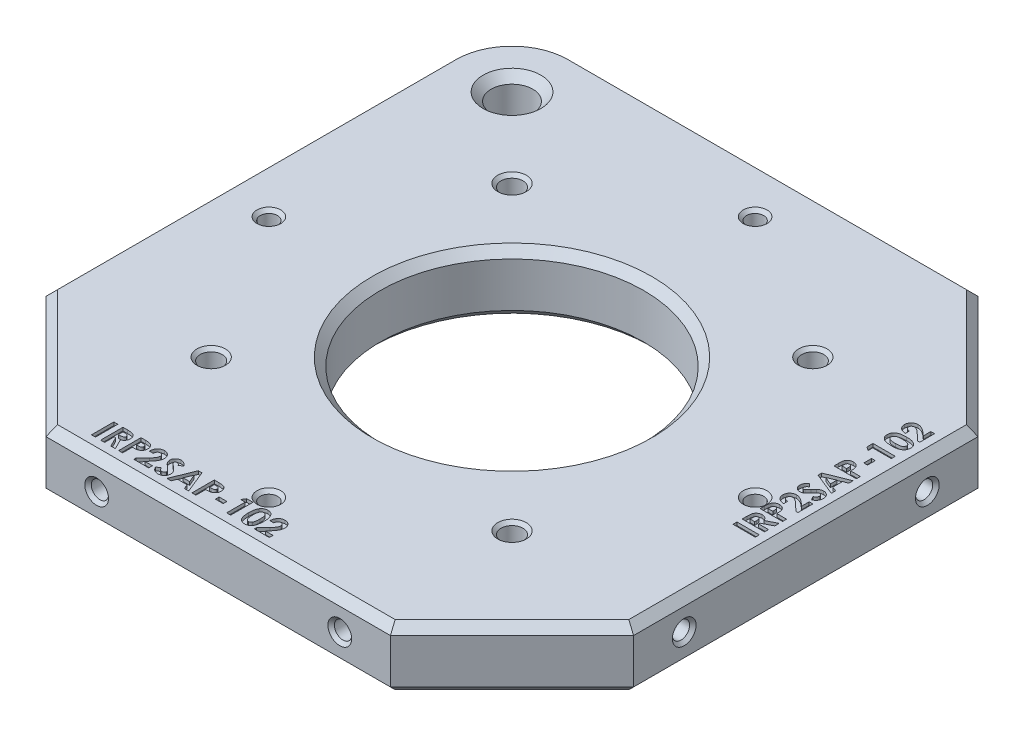
SolidWorks part; units mm, degrees
material "6061-T6 (SS)"
ref_plane "Front" through (0, 0, 0) normal (0, 0, 1) x (1, 0, 0)
ref_plane "Top" through (0, 0, 0) normal (0, 1, 0) x (1, 0, 0)
ref_plane "Right" through (0, 0, 0) normal (1, 0, 0) x (0, 0, -1)
sketch "Sketch1" plane through (0, 0, 0) normal (0, 1, 0) x (1, 0, 0)
  line L0 (0, 46.0375) -> (46.0375, 46.0375) construction
  line L1 (0, 0) -> (92.075, 0)
  line L2 (0, 0) -> (0, 92.075)
  line L3 (0, 92.075) -> (92.075, 92.075)
  line L4 (92.075, 0) -> (92.075, 92.075)
  line L5 (46.0375, 46.0375) -> (46.0375, 92.075) construction
  line L6 (10.033, 82.042) -> (0, 82.042) construction
  line L7 (10.033, 82.042) -> (10.033, 92.075) construction
  line L9 (17.3653, 82.042) -> (13.6992, 88.392) construction
  line L10 (13.6992, 88.392) -> (6.3668, 88.392) construction
  line L11 (6.3668, 88.392) -> (2.7007, 82.042) construction
  line L12 (2.7007, 82.042) -> (6.3668, 75.692) construction
  line L13 (6.3668, 75.692) -> (13.6992, 75.692) construction
  line L14 (13.6992, 75.692) -> (17.3653, 82.042) construction
  circle A0 centre (46.0375, 46.0375) radius 20.6375
  circle A1 centre (10.033, 82.042) radius 4.6037 construction
  circle A2 centre (10.033, 82.042) radius 6.35 construction
  dimension "D2" = 41.275
  dimension "D3" = 9.2075
  dimension "D1" = 92.075
  dimension "D4" = 10.033
  dimension "D5" = 12.7
extrude "Boss-Extrude1" add sketch "Sketch1" along normal blind 9.525
hole_wizard "5/16-18 Tapped Hole1" positions "Sketch9" profile "Sketch10" tap size "5/16-18" standard "ANSI Inch" end condition through all
sketch "Sketch9" plane through (0, 9.525, 0) normal (0, 1, 0) x (1, 0, 0)
  circle A0 centre (10.033, 82.042) radius 4.6037 construction
  point P0 (10.033, 82.042)
sketch "Sketch10" plane through (10.033, 9.525, -82.042) normal (1, 0, 0) x (0, 0, 1)
  line L0 (0, 0) -> (0, 9.525)
  line L1 (0, 9.525) -> (3.2639, 9.525)
  line L2 (3.2639, 9.525) -> (3.2639, 0)
  line L5 (3.2639, 0) -> (0, 0)
  line L11 (0, -6.35) -> (0, 107.95) construction
  dimension "Thru Tap Drill Dia." = 6.5278
  dimension "Thru Tap Drill Depth" = 9.525
cosmetic thread "Hole Thread13" parameters "D2"=7.9375
chamfer "Chamfer1" distance 19.05 angle 45 3 edges at (92.075, 4.7625, 0) (0, 4.7625, 0) (92.075, 4.7625, -92.075)
hole_wizard "#6-32 Tapped Hole1" positions "Sketch2" profile "Sketch3" tap size "#6-32" standard "ANSI Inch"
sketch "Sketch2" plane through (0, 0, 0) normal (0, 0, 1) x (1, 0, 0)
  line L6 (0, 4.7625) -> (26.9875, 4.7625) construction
  line L7 (0, 9.525) -> (0, 0) construction
  line L8 (26.9875, 4.7625) -> (65.0875, 4.7625) construction
  line L9 (65.0875, 4.7625) -> (92.075, 4.7625) construction
  line L10 (92.075, 9.525) -> (92.075, 0) construction
  point P26 (26.9875, 4.7625)
  point P30 (65.0875, 4.7625)
  dimension "D1" = 38.1
sketch "Sketch3" plane through (65.0875, 4.7625, 0) normal (1, 0, 0) x (0, -1, 0)
  line L0 (0, 0) -> (0, 13.5127)
  line L1 (0, 13.5127) -> (1.3525, 12.7)
  line L2 (1.3525, 12.7) -> (1.3525, 0)
  line L5 (1.3525, 0) -> (0, 0)
  line L10 (0, 13.5127) -> (-1.3526, 12.7) construction
  line L11 (0, -6.35) -> (0, 107.95) construction
  dimension "Tap Drill Dia." = 2.7051
  dimension "Tap Drill Depth" = 12.7
  dimension "Drill Angle" = 118
cosmetic thread "Hole Thread1" parameters "D1"=11.43, "D2"=3.5052
cosmetic thread "Hole Thread2" parameters "D1"=11.43, "D2"=3.5052
ref_plane "Plane1" through (46.0375, 0, -46.0375) normal (-0.7071, 0, 0.7071) x (0.7071, 0, 0.7071)
mirror "Mirror1" about plane through (46.0375, 0, -46.0375) normal (-0.7071, 0, 0.7071) of "#6-32 Tapped Hole1"
cosmetic thread "Hole Thread3" parameters "D1"=11.43, "D2"=3.5052
cosmetic thread "Hole Thread4" parameters "D1"=11.43, "D2"=3.5052
fillet "Fillet1" radius 10.033 1 edges at (0, 4.7625, -92.075)
chamfer "Chamfer2" distance 1.27 angle 45 18 edges at (46.0375, 0, -25.4) (46.0375, 9.525, -25.4) (0, 0, -50.546) (41.529, 0, -92.075) (92.075, 0, -46.0375) (82.55, 0, -9.525) (46.0375, 0, 0) (0, 9.525, -50.546) (41.529, 9.525, -92.075) (92.075, 9.525, -46.0375) (82.55, 9.525, -9.525) (46.0375, 9.525, 0) (82.55, 9.525, -82.55) (9.525, 9.525, -9.525) (2.9386, 9.525, -89.1364) (2.9386, 0, -89.1364) (10.033, 9.525, -78.7781) (10.033, 0, -78.7781)
hole_wizard "#8-32 Tapped Hole1" positions "Sketch5" profile "Sketch6" tap size "#8-32" standard "ANSI Inch" end condition through all
sketch "Sketch5" plane through (0, 9.525, 0) normal (0, 1, 0) x (1, 0, 0)
  line L1 (22.4663, 22.4663) -> (69.6087, 22.4663) construction
  line L2 (22.4663, 22.4663) -> (22.4663, 69.6087) construction
  line L3 (22.4663, 69.6087) -> (69.6087, 69.6087) construction
  line L4 (69.6087, 22.4663) -> (69.6087, 69.6087) construction
  line L6 (22.4663, 22.4663) -> (46.0375, 46.0375) construction
  line L7 (46.0375, 46.0375) -> (69.6087, 69.6087) construction
  point P2 (69.6087, 69.6087)
  point P73 (22.4663, 69.6087)
  point P74 (69.6087, 22.4663)
  point P84 (22.4663, 22.4663)
  dimension "D1" = 47.1424
sketch "Sketch6" plane through (22.4663, 9.525, -22.4663) normal (1, 0, 0) x (0, 0, 1)
  line L0 (0, 0) -> (0, 9.525)
  line L1 (0, 9.525) -> (1.7272, 9.525)
  line L2 (1.7272, 9.525) -> (1.7272, 0)
  line L5 (1.7272, 0) -> (0, 0)
  line L11 (0, -6.35) -> (0, 107.95) construction
  dimension "Thru Tap Drill Dia." = 3.4544
  dimension "Thru Tap Drill Depth" = 9.525
cosmetic thread "Hole Thread5" parameters "D2"=4.1656
cosmetic thread "Hole Thread6" parameters "D2"=4.1656
cosmetic thread "Hole Thread7" parameters "D2"=4.1656
cosmetic thread "Hole Thread8" parameters "D2"=4.1656
sketch "Sketch4" plane through (0, 9.525, 0) normal (0, 1, 0) x (1, 0, 0)
  line L0 (1.27, 2.54) -> (73.7689, 2.54) construction
  line L1 (1.27, 82.042) -> (1.27, 19.5761) construction
  line L2 (72.4989, 1.27) -> (90.805, 19.5761) construction
  line L3 (89.535, 18.3061) -> (89.535, 90.805) construction
  line L4 (72.4989, 90.805) -> (10.033, 90.805) construction
  line L5 (90.805, 19.5761) -> (90.805, 72.4989) construction
  text T0 "<b>IRP2SAP-102</b>"
  text T1 "<b>IRP2SAP-102</b>"
  dimension "D1" = 1.27
extrude "Cut-Extrude1" cut sketch "Sketch4" against normal blind 0.508
hole_wizard "#6-32 Tapped Hole2" positions "Sketch7" profile "Sketch8" tap size "#6-32" standard "ANSI Inch" end condition through all
sketch "Sketch7" plane through (0, 9.525, 0) normal (0, 1, 0) x (1, 0, 0)
  line L0 (7.9375, 46.0375) -> (46.0375, 84.1375) construction
  line L1 (46.0375, 84.1375) -> (84.1375, 46.0375) construction
  line L2 (84.1375, 46.0375) -> (46.0375, 7.9375) construction
  line L3 (46.0375, 7.9375) -> (7.9375, 46.0375) construction
  line L4 (7.9375, 46.0375) -> (46.0375, 46.0375) construction
  line L5 (46.0375, 46.0375) -> (84.1375, 46.0375) construction
  line L7 (46.0375, 7.9375) -> (46.0375, 46.0375) construction
  line L8 (46.0375, 46.0375) -> (46.0375, 84.1375) construction
  point P0 (7.9375, 46.0375)
  point P2 (46.0375, 7.9375)
  point P4 (84.1375, 46.0375)
  point P6 (46.0375, 84.1375)
  point P27 (0, 0)
  dimension "D1" = 76.2
sketch "Sketch8" plane through (7.9375, 9.525, -46.0375) normal (1, 0, 0) x (0, 0, 1)
  line L0 (0, 0) -> (0, 9.525)
  line L1 (0, 9.525) -> (1.3525, 9.525)
  line L2 (1.3525, 9.525) -> (1.3525, 0)
  line L5 (1.3525, 0) -> (0, 0)
  line L11 (0, -6.35) -> (0, 107.95) construction
  dimension "Thru Tap Drill Dia." = 2.7051
  dimension "Thru Tap Drill Depth" = 9.525
cosmetic thread "Hole Thread9" parameters "D2"=3.5052
cosmetic thread "Hole Thread10" parameters "D2"=3.5052
cosmetic thread "Hole Thread11" parameters "D2"=3.5052
cosmetic thread "Hole Thread12" parameters "D2"=3.5052
chamfer "Chamfer3" distance 0.508 angle 45 20 edges at (92.075, 4.7625, -66.4401) (92.075, 4.7625, -28.34) (66.44, 4.7625, 0) (28.34, 4.7625, 0) (69.6087, 9.525, -20.7391) (69.6087, 0, -20.7391) (69.6087, 9.525, -67.8815) (69.6087, 0, -67.8815) (22.4663, 9.525, -67.8815) (22.4663, 0, -67.8815) (22.4663, 9.525, -20.7391) (22.4663, 0, -20.7391) (84.1375, 9.525, -44.685) (84.1375, 0, -44.685) (46.0375, 9.525, -82.7849) (46.0375, 0, -82.785) (46.0375, 9.525, -6.5849) (46.0375, 0, -6.585) (7.9375, 9.525, -44.685) (7.9375, 0, -44.685)
